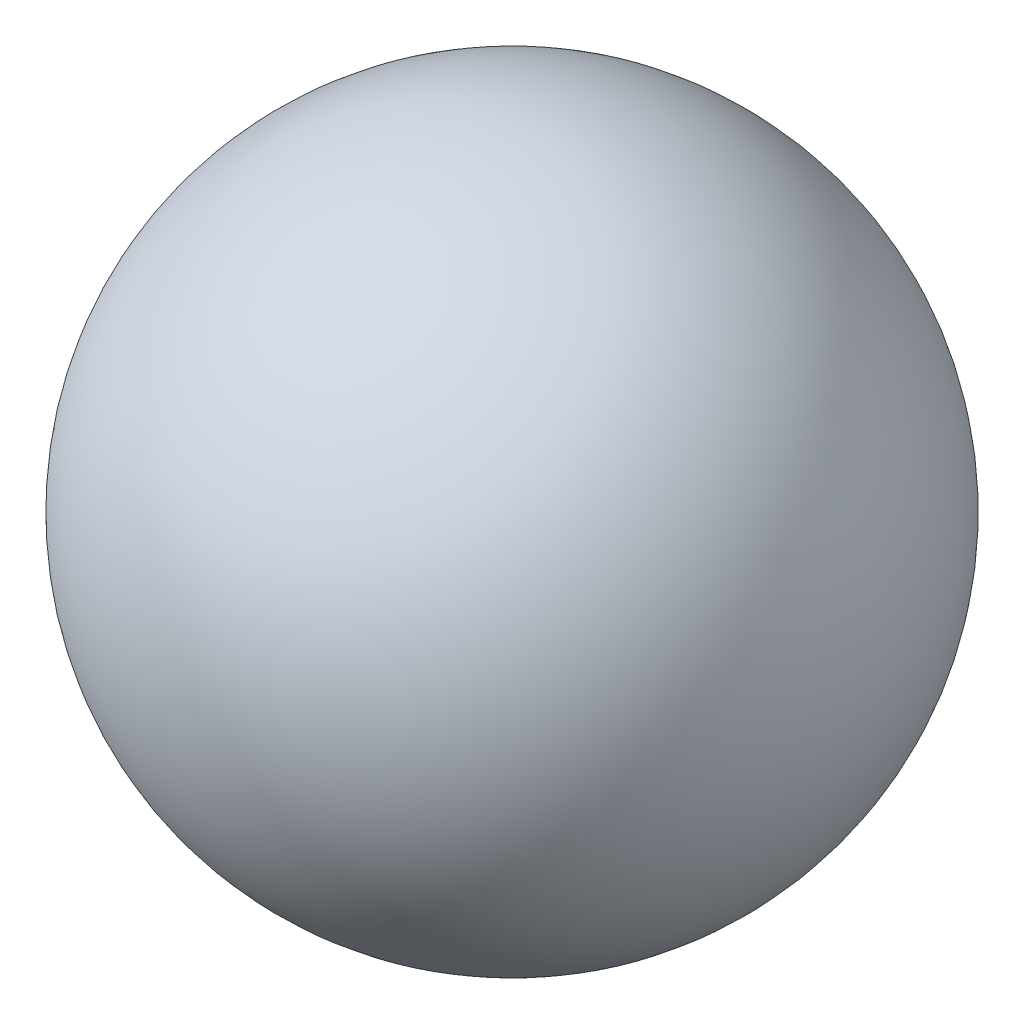
SolidWorks part; units mm, degrees
ref_plane "Front Plane" through (0, 0, 0) normal (0, 0, 1) x (1, 0, 0)
ref_plane "Top Plane" through (0, 0, 0) normal (0, 1, 0) x (1, 0, 0)
ref_plane "Right Plane" through (0, 0, 0) normal (1, 0, 0) x (0, 0, -1)
sketch "Sketch1" plane through (0, 0, 0) normal (0, 0, 1) x (1, 0, 0)
  line L0 (0, 0) -> (0, -12.7) construction
  line L1 (0, 0) -> (0, 12.7) construction
  line L2 (0, 12.7) -> (0, -12.7)
  arc A0 (0, -12.7) -> (0, 12.7) centre (0, 0) ccw
  dimension "D1" = 25.4
revolve "Revolve4" add sketch "Sketch1" angle 360 about L2
